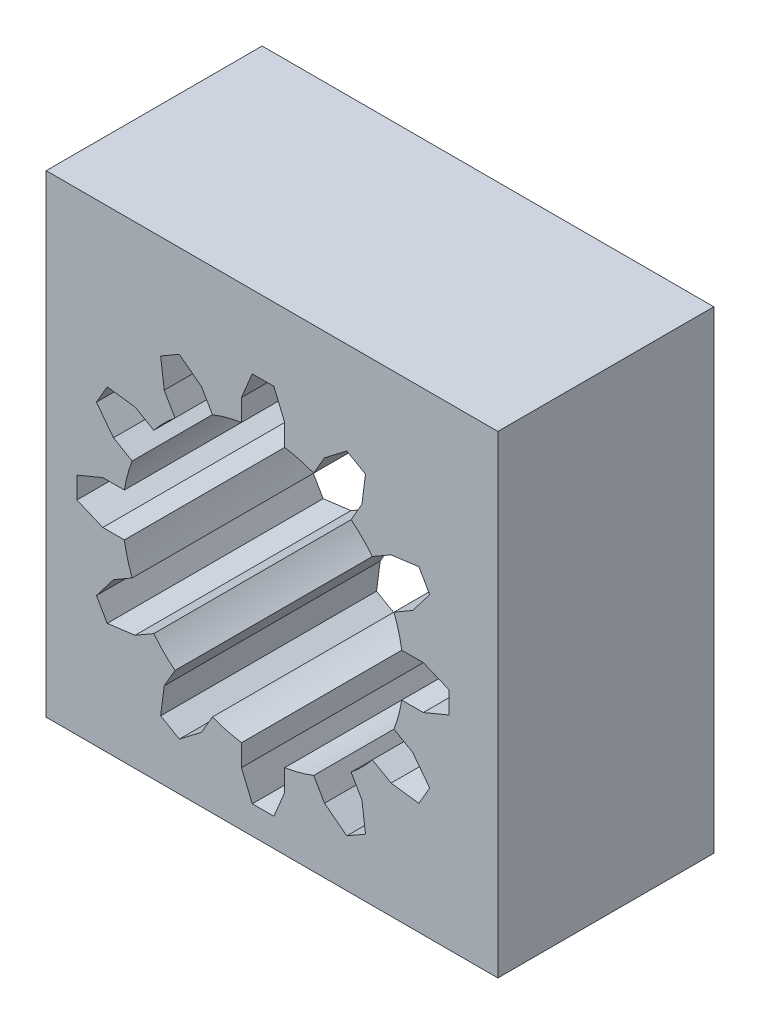
SolidWorks part; units mm, degrees
ref_plane "Front Plane" through (0, 0, 0) normal (0, 0, 1) x (1, 0, 0)
ref_plane "Top Plane" through (0, 0, 0) normal (0, 1, 0) x (1, 0, 0)
ref_plane "Right Plane" through (0, 0, 0) normal (1, 0, 0) x (0, 0, -1)
sketch "Sketch1" plane through (0, 0, 0) normal (0, 0, 1) x (1, 0, 0)
  line L0 (0, 0) -> (0, 8.6226) construction
  line L1 (-1, 6.4226) -> (-1, 7.4226)
  line L2 (-1, 7.4226) -> (-0.5, 8.6226)
  line L3 (-0.5, 8.6226) -> (0.5, 8.6226)
  line L4 (0.5, 8.6226) -> (1, 7.4226)
  line L5 (1, 7.4226) -> (1, 6.4226)
  line L6 (2.8453, 6.9282) -> (3.8783, 7.7174)
  line L7 (3.8783, 7.7174) -> (4.7443, 7.2174)
  line L8 (4.7443, 7.2174) -> (4.5773, 5.9282)
  line L9 (4.5773, 5.9282) -> (4.0773, 5.0621)
  line L10 (2.3453, 6.0621) -> (2.8453, 6.9282)
  line L11 (5.9282, 4.5773) -> (7.2174, 4.7443)
  line L12 (7.2174, 4.7443) -> (7.7174, 3.8783)
  line L13 (7.7174, 3.8783) -> (6.9282, 2.8453)
  line L14 (6.9282, 2.8453) -> (6.0621, 2.3453)
  line L15 (5.0621, 4.0773) -> (5.9282, 4.5773)
  line L16 (7.4226, 1) -> (8.6226, 0.5)
  line L17 (8.6226, 0.5) -> (8.6226, -0.5)
  line L18 (8.6226, -0.5) -> (7.4226, -1)
  line L19 (7.4226, -1) -> (6.4226, -1)
  line L20 (6.4226, 1) -> (7.4226, 1)
  line L21 (6.9282, -2.8453) -> (7.7174, -3.8783)
  line L22 (7.7174, -3.8783) -> (7.2174, -4.7443)
  line L23 (7.2174, -4.7443) -> (5.9282, -4.5773)
  line L24 (5.9282, -4.5773) -> (5.0621, -4.0773)
  line L25 (6.0621, -2.3453) -> (6.9282, -2.8453)
  line L26 (4.5773, -5.9282) -> (4.7443, -7.2174)
  line L27 (4.7443, -7.2174) -> (3.8783, -7.7174)
  line L28 (3.8783, -7.7174) -> (2.8453, -6.9282)
  line L29 (2.8453, -6.9282) -> (2.3453, -6.0621)
  line L30 (4.0773, -5.0621) -> (4.5773, -5.9282)
  line L31 (1, -7.4226) -> (0.5, -8.6226)
  line L32 (0.5, -8.6226) -> (-0.5, -8.6226)
  line L33 (-0.5, -8.6226) -> (-1, -7.4226)
  line L34 (-1, -7.4226) -> (-1, -6.4226)
  line L35 (1, -6.4226) -> (1, -7.4226)
  line L36 (-2.8453, -6.9282) -> (-3.8783, -7.7174)
  line L37 (-3.8783, -7.7174) -> (-4.7443, -7.2174)
  line L38 (-4.7443, -7.2174) -> (-4.5773, -5.9282)
  line L39 (-4.5773, -5.9282) -> (-4.0773, -5.0621)
  line L40 (-2.3453, -6.0621) -> (-2.8453, -6.9282)
  line L41 (-5.9282, -4.5773) -> (-7.2174, -4.7443)
  line L42 (-7.2174, -4.7443) -> (-7.7174, -3.8783)
  line L43 (-7.7174, -3.8783) -> (-6.9282, -2.8453)
  line L44 (-6.9282, -2.8453) -> (-6.0621, -2.3453)
  line L45 (-5.0621, -4.0773) -> (-5.9282, -4.5773)
  line L46 (-7.4226, -1) -> (-8.6226, -0.5)
  line L47 (-8.6226, -0.5) -> (-8.6226, 0.5)
  line L48 (-8.6226, 0.5) -> (-7.4226, 1)
  line L49 (-7.4226, 1) -> (-6.4226, 1)
  line L50 (-6.4226, -1) -> (-7.4226, -1)
  line L51 (-6.9282, 2.8453) -> (-7.7174, 3.8783)
  line L52 (-7.7174, 3.8783) -> (-7.2174, 4.7443)
  line L53 (-7.2174, 4.7443) -> (-5.9282, 4.5773)
  line L54 (-5.9282, 4.5773) -> (-5.0621, 4.0773)
  line L55 (-6.0621, 2.3453) -> (-6.9282, 2.8453)
  line L56 (-4.5773, 5.9282) -> (-4.7443, 7.2174)
  line L57 (-4.7443, 7.2174) -> (-3.8783, 7.7174)
  line L58 (-3.8783, 7.7174) -> (-2.8453, 6.9282)
  line L59 (-2.8453, 6.9282) -> (-2.3453, 6.0621)
  line L60 (-4.0773, 5.0621) -> (-4.5773, 5.9282)
  line L62 (-10.0431, 11.9998) -> (10.8743, 11.9998)
  line L63 (-10.0431, 11.9998) -> (-10.0431, -9.9219)
  line L64 (-10.0431, -9.9219) -> (10.8743, -9.9219)
  line L65 (10.8743, 11.9998) -> (10.8743, -9.9219)
  circle A0 centre (0, 0) radius 4.5
  arc A1 (-4.0773, 5.0621) -> (-5.0621, 4.0773) centre (0, 0) ccw
  arc A2 (-6.0621, 2.3453) -> (-6.4226, 1) centre (0, 0) ccw
  arc A3 (-6.4226, -1) -> (-6.0621, -2.3453) centre (0, 0) ccw
  arc A4 (-5.0621, -4.0773) -> (-4.0773, -5.0621) centre (0, 0) ccw
  arc A5 (-2.3453, -6.0621) -> (-1, -6.4226) centre (0, 0) ccw
  arc A6 (1, -6.4226) -> (2.3453, -6.0621) centre (0, 0) ccw
  arc A7 (4.0773, -5.0621) -> (5.0621, -4.0773) centre (0, 0) ccw
  arc A8 (6.0621, -2.3453) -> (6.4226, -1) centre (0, 0) ccw
  arc A9 (6.4226, 1) -> (6.0621, 2.3453) centre (0, 0) ccw
  arc A10 (5.0621, 4.0773) -> (4.0773, 5.0621) centre (0, 0) ccw
  arc A11 (2.3453, 6.0621) -> (1, 6.4226) centre (0, 0) ccw
  arc A12 (-1, 6.4226) -> (-2.3453, 6.0621) centre (0, 0) ccw
  point P80 (0, 0)
  dimension "D1" = 12
extrude "Boss-Extrude1" add sketch "Sketch1" along normal mid plane 10 contours L65 L62 L63 L64 A1 L20 L16 L17 L18 L19 L25 L21 L22 L23 L24 L30 L26 L27 L28 L29 L35 L31 L32 L33 L34 L40 L36 L37 L38 L39 L45 L41 L42 L43 L44 L50 L46 L47 L48 L49 L55 L51 L52
